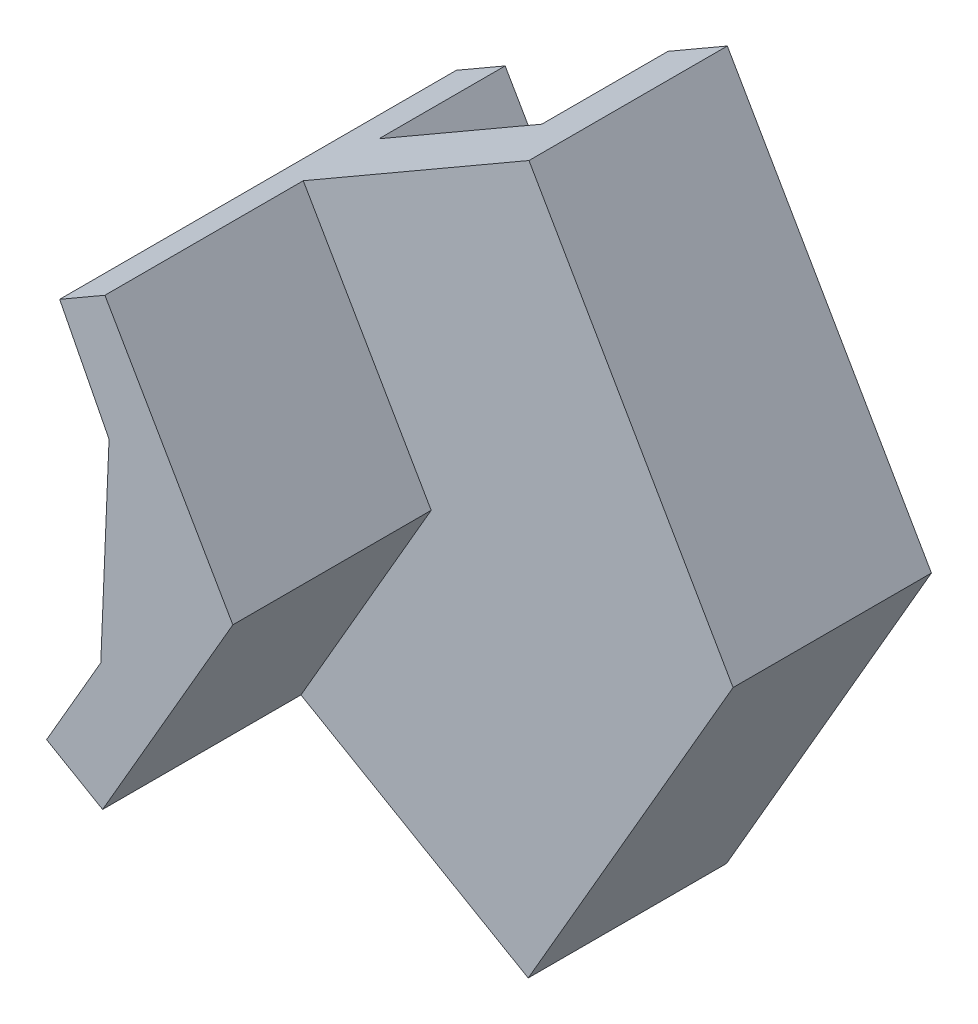
SolidWorks part; units mm, degrees
ref_plane "Alzado" through (0, 0, 0) normal (0, 0, 1) x (1, 0, 0)
ref_plane "Planta" through (0, 0, 0) normal (0, 1, 0) x (1, 0, 0)
ref_plane "Vista lateral" through (0, 0, 0) normal (1, 0, 0) x (0, 0, -1)
sketch "Croquis1" plane through (0, 0, 0) normal (0, 0, 1) x (1, 0, 0)
  line L0 (94.6312, -5.2106) -> (102.4862, -9.7568)
  line L1 (102.4862, -9.7568) -> (108.1671, 0.0587)
  line L2 (108.1671, 0.0587) -> (102.5075, 9.8854)
  line L3 (102.5075, 9.8854) -> (94.9938, 5.5457)
  line L4 (94.9938, 5.5457) -> (96.3634, 2.8723)
  line L5 (96.3634, 2.8723) -> (96.1339, -2.6141)
  line L6 (96.1339, -2.6141) -> (94.6312, -5.2106)
extrude "Saliente-Extruir1" add sketch "Croquis1" along normal blind 2
sketch "Croquis2" plane through (0, 0, 0) normal (0, 0, -1) x (-1, 0, 0)
  line L0 (-96.3412, -6.2003) -> (-100.8418, -8.805)
  line L1 (-94.6312, -5.2106) -> (-102.4862, -9.7568) construction
  line L2 (-96.3412, -6.2003) -> (-99.9739, 0.0763) construction
  line L3 (-100.8418, -8.805) -> (-105.9805, 0.0736) construction
  line L4 (-100.8418, -8.805) -> (-105.9805, 0.0736)
  line L5 (-105.9805, 0.0736) -> (-100.8622, 8.9352)
  line L6 (-102.5075, 9.8854) -> (-94.9938, 5.5457) construction
  line L7 (-100.8622, 8.9352) -> (-105.9805, 0.0736) construction
  line L8 (-100.8622, 8.9352) -> (-96.347, 6.3272)
  line L9 (-55.35, 77.3361) -> (-100, 0) construction
  line L10 (-96.347, 6.3272) -> (-100, 0)
  line L11 (-100, 0) -> (-96.3412, -6.2003)
  line L12 (-96.3412, -6.2003) -> (-94.6312, -5.2106)
  line L13 (-94.6312, -5.2106) -> (-96.1339, -2.6141)
  line L14 (-96.1339, -2.6141) -> (-96.3634, 2.8723)
  line L15 (-96.3634, 2.8723) -> (-94.9938, 5.5457)
  line L16 (-94.9938, 5.5457) -> (-96.347, 6.3272)
  line L17 (-100.8418, -8.805) -> (-102.4862, -9.7568)
  line L18 (-102.4862, -9.7568) -> (-108.1671, 0.0587)
  line L19 (-108.1671, 0.0587) -> (-102.5075, 9.8854)
  line M1 (-94.6312, -5.2106) -> (-96.1339, -2.6141)
  line M2 (-96.1339, -2.6141) -> (-96.3634, 2.8723)
  line M3 (-96.3634, 2.8723) -> (-94.9938, 5.5457)
  line M4 (-94.9938, 5.5457) -> (-102.5075, 9.8854)
  line M5 (-102.5075, 9.8854) -> (-108.1671, 0.0587)
  line M6 (-108.1671, 0.0587) -> (-102.4862, -9.7568)
  line M7 (-102.4862, -9.7568) -> (-94.6312, -5.2106)
extrude "Saliente-Extruir2" add sketch "Croquis2" along normal blind 3.5 contours L10 L11 M7 M1 M2 M3 M4 | L4 L5 M4 M5 M6 M7
sketch "Croquis3" plane through (0, 0, 2) normal (0, 0, 1) x (1, 0, 0)
  line L0 (94.6312, -5.2106) -> (96.1339, -2.6141)
  line L1 (96.1339, -2.6141) -> (96.3634, 2.8723)
  line L2 (96.3634, 2.8723) -> (94.9938, 5.5457)
  line L3 (94.9938, 5.5457) -> (96.2487, 6.2705)
  line L4 (102.5075, 9.8854) -> (94.9938, 5.5457) construction
  line L5 (96.2487, 6.2705) -> (99.7958, 0.1291)
  line L6 (99.7958, 0.1291) -> (96.185, -6.1098)
  line L7 (94.6312, -5.2106) -> (102.4862, -9.7568) construction
  line L8 (96.185, -6.1098) -> (94.6312, -5.2106)
extrude "Saliente-Extruir3" add sketch "Croquis3" along normal blind 5.5
